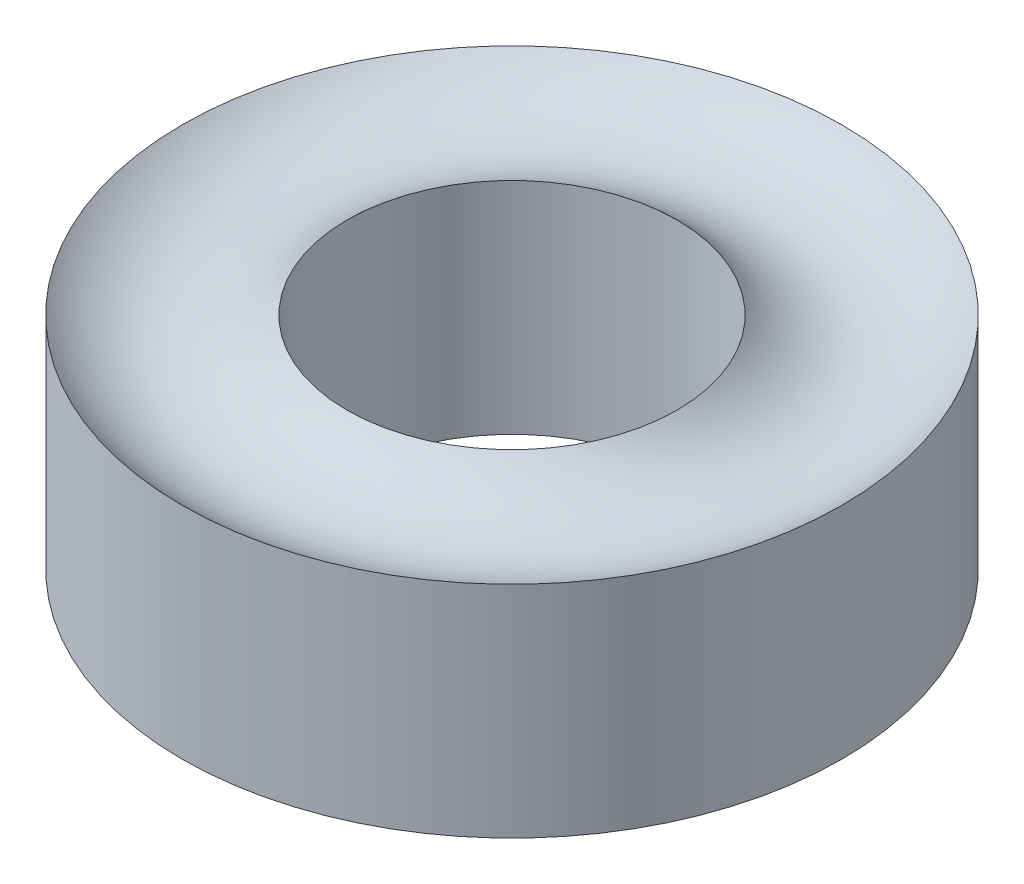
SolidWorks part; units mm, degrees
material "AISI 304"
ref_plane "Front Plane" through (0, 0, 0) normal (0, 0, 1) x (1, 0, 0)
ref_plane "Top Plane" through (0, 0, 0) normal (0, 1, 0) x (1, 0, 0)
ref_plane "Right Plane" through (0, 0, 0) normal (1, 0, 0) x (0, 0, -1)
sketch "Sketch2" plane through (0, 0, 0) normal (0, 0, 1) x (1, 0, 0)
  line L0 (0, 0) -> (0, 48.1351) construction
  line L1 (0, 0) -> (1.5, 0) construction
  line L2 (1.5, 0) -> (1.5, 2)
  line L3 (3, 2) -> (3, 0)
  line L4 (3, 0) -> (1.5, 0) construction
  line L5 (1.5, 2) -> (3, 2) construction
  line L6 (2.25, 2.75) -> (2.25, -0.75) construction
  line L7 (3, 0) -> (12.146, -9.146) construction
  arc A0 (1.5, 2) -> (3, 2) centre (2.25, 2.75) ccw
  arc A1 (1.5, 0) -> (3, 0) centre (2.25, -0.75) cw
  dimension "D1" = 45
  dimension "D2" = 2
  dimension "D3" = 3
  dimension "D4" = 6
revolve "Revolve1" add sketch "Sketch2" angle 360 about L0
